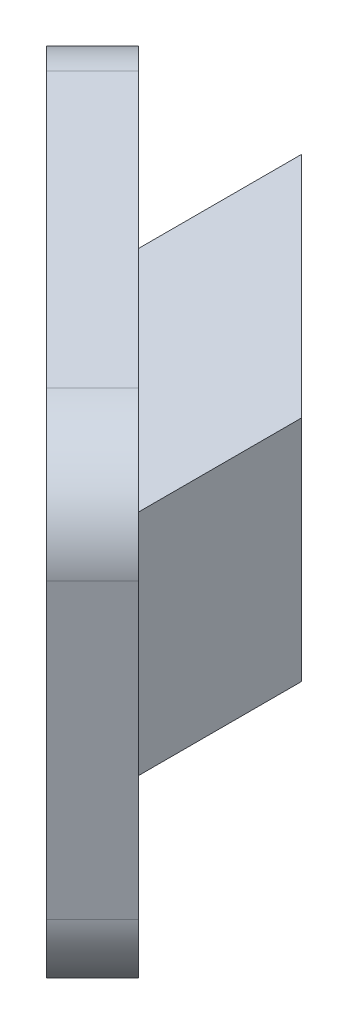
SolidWorks part; units mm, degrees
ref_plane "Front Plane" through (0, 0, 0) normal (0, 0, 1) x (1, 0, 0)
ref_plane "Top Plane" through (0, 0, 0) normal (0, 1, 0) x (1, 0, 0)
ref_plane "Right Plane" through (0, 0, 0) normal (1, 0, 0) x (0, 0, -1)
sketch "Sketch1" plane through (0, 0, 0) normal (0, 0, 1) x (1, 0, 0)
  line L1 (-3.5, 3.5) -> (3.5, 3.5)
  line L2 (-3.5, 3.5) -> (-3.5, -3.5)
  line L3 (-3.5, -3.5) -> (3.5, -3.5)
  line L4 (3.5, 3.5) -> (3.5, -3.5)
  line L5 (-3.5, 3.5) -> (3.5, -3.5) construction
  line L6 (-3.5, -3.5) -> (3.5, 3.5) construction
  circle A0 centre (0, 0) radius 3
  point P0 (0, 0)
  dimension "D2" = 6
  dimension "D1" = 7
extrude "Boss-Extrude1" add sketch "Sketch1" along normal blind 12
sketch "Sketch3" plane through (0, 3.5, 0) normal (0, 1, 0) x (1, 0, 0)
  line L8 (-3.5, -12) -> (3.5, -12)
  line L9 (3.5, -12) -> (-3.5, -5)
  line L10 (-3.5, -12) -> (-3.5, 0) construction
  line L11 (-3.5, -5) -> (-3.5, -12)
  dimension "D1" = 45
extrude "Cut-Extrude1" cut sketch "Sketch3" against normal through all
sketch "Sketch5" plane through (-4.25, 0, 4.25) normal (-0.7071, 0, 0.7071) x (0.7071, 0, 0.7071)
  line L8 (14.9602, 7.5) -> (-2.9393, 7.5)
  line L9 (-2.9393, 7.5) -> (-2.9393, -7.5)
  line L10 (-2.9393, -7.5) -> (14.9602, -7.5)
  line L11 (14.9602, -7.5) -> (14.9602, 7.5)
  line L12 (14.9602, 7.5) -> (-2.9393, 7.5)
  line L13 (-2.9393, 7.5) -> (-2.9393, -7.5)
  line L14 (-2.9393, -7.5) -> (14.9602, -7.5)
  line L15 (14.9602, -7.5) -> (14.9602, 7.5)
  dimension "D1" = 4
extrude "Boss-Extrude3" add sketch "Sketch5" along normal blind 2
sketch "Sketch7" plane through (0, 0, 0) normal (0, 0, -1) x (-1, 0, 0)
  circle A0 centre (0, 0) radius 3 construction
  circle A1 centre (0, 0) radius 3
extrude "Cut-Extrude3" cut sketch "Sketch7" against normal through all
sketch "Sketch6" plane through (0, 3.5, 0) normal (0, 1, 0) x (1, 0, 0)
  line L0 (-3.5, 0) -> (3.5, -7)
  line L1 (3.5, 0) -> (-3.5, 0) construction
  line L2 (3.5, -12) -> (3.5, 0) construction
  line L3 (3.5, -12) -> (-3.5, -5) construction
  line L4 (3.5, -7) -> (3.5, 0)
  line L5 (3.5, 0) -> (-3.5, 0)
  point P8 (3.5, -7.6632)
  point P11 (-3.5, 0)
extrude "Cut-Extrude2" cut sketch "Sketch6" against normal through all
fillet "Fillet3" radius 3 4 edges at (5.6213, -7.5, 15.5355) (-7.0355, -7.5, 2.8787) (-7.0355, 7.5, 2.8787) (5.6213, 7.5, 15.5355)
